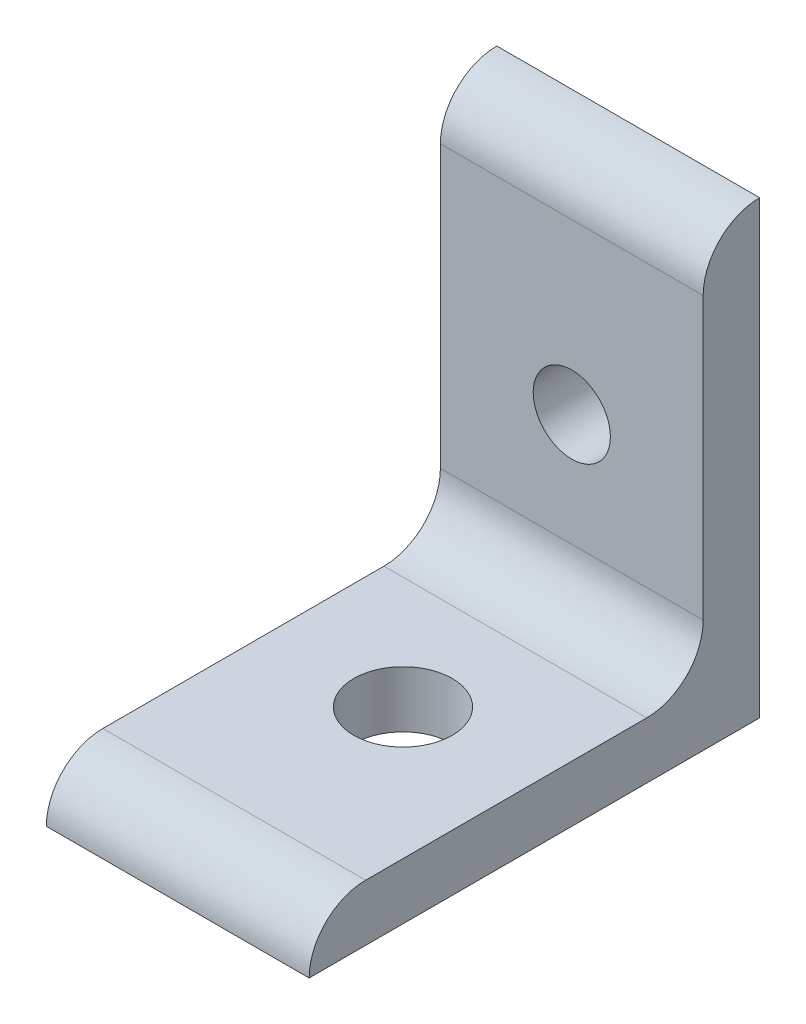
SolidWorks part; units mm, degrees
ref_plane "Front"
ref_plane "Top" through (0, 0, 0) normal (0, 1, 0) x (1, 0, 0)
ref_plane "Right" through (0, 0, 0) normal (1, 0, 0) x (0, 0, -1)
sketch "Sketch1" plane through (0, 0, 0) normal (1, 0, 0) x (0, 0, -1)
  line L0 (-4.7752, 9.5504) -> (-4.7752, 33.3248)
  line L1 (-33.3248, 4.7752) -> (-9.5504, 4.7752)
  line L6 (0, 0) -> (0, 38.1)
  line L7 (-38.1, 0) -> (0, 0)
  arc A0 (-9.5504, 4.7752) -> (-4.7752, 9.5504) centre (-9.5504, 9.5504) ccw
  arc A1 (0, 38.1) -> (-4.7752, 33.3248) centre (0, 33.3248) ccw
  arc A2 (-33.3248, 4.7752) -> (-38.1, 0) centre (-33.3248, 0) ccw
  dimension "InnerRadius" = 4.7752
  dimension "LengthZ" = 38.1
  dimension "HeightY" = 38.1
  dimension "Thick" = 4.7752
extrude "Base Extrude" add sketch "Sketch1" against normal mid plane 22.225
sketch "Sketch2" plane through (0, 0, 0) normal (0, -1, 0) x (1, 0, 0)
  line L0 (-11.1125, 0) -> (11.1125, 0) construction
  line L1 (-11.1125, 38.1) -> (-11.1125, 0) construction
  circle A1 centre (0, 19.05) radius 4.1656
  dimension "Hole1Diam" = 8.3312
  dimension "Hole1Z" = 19.05
  dimension "Hole1X" = 11.1125
extrude "Hole1" cut sketch "Sketch2" against normal through all
pattern_linear "Hole1 Pattern" [suppressed]
sketch "Sketch3" plane through (0, 0, 0) normal (0, 0, -1) x (-1, 0, 0)
  line L0 (11.1125, 0) -> (-11.1125, 0) construction
  line L1 (11.1125, 0) -> (11.1125, 38.1) construction
  circle A0 centre (0, 19.05) radius 3.2639
  dimension "Hole2Diam" = 6.5278
  dimension "Hole2Y" = 19.05
  dimension "Hole2X" = 11.1125
extrude "Hole2" cut sketch "Sketch3" against normal through all
pattern_linear "Hole2 Pattern" [suppressed]
sketch "Sketch4" plane through (0, 0, 0) normal (0, 0, -1) x (-1, 0, 0)
  line L0 (11.1125, 38.1) -> (11.1125, 6.35)
  line L1 (11.1125, 0) -> (11.1125, 38.1) construction
  line L2 (11.1125, 6.35) -> (19.05, 38.1)
  line L3 (11.1125, 38.1) -> (-11.1125, 38.1) construction
  line L4 (19.05, 38.1) -> (11.1125, 38.1)
  line L5 (0, 38.1) -> (0, 0) construction
  line L6 (11.1125, 0) -> (-11.1125, 0) construction
  line L7 (-11.1125, 38.1) -> (-11.1125, 6.35)
  line L8 (-11.1125, 6.35) -> (-19.05, 38.1)
  line L9 (-19.05, 38.1) -> (-11.1125, 38.1)
  dimension "CornerX" = 38.1
  dimension "CornerY" = 6.35
extrude "Corner Cut" [suppressed] cut sketch "Sketch4" against normal through all
